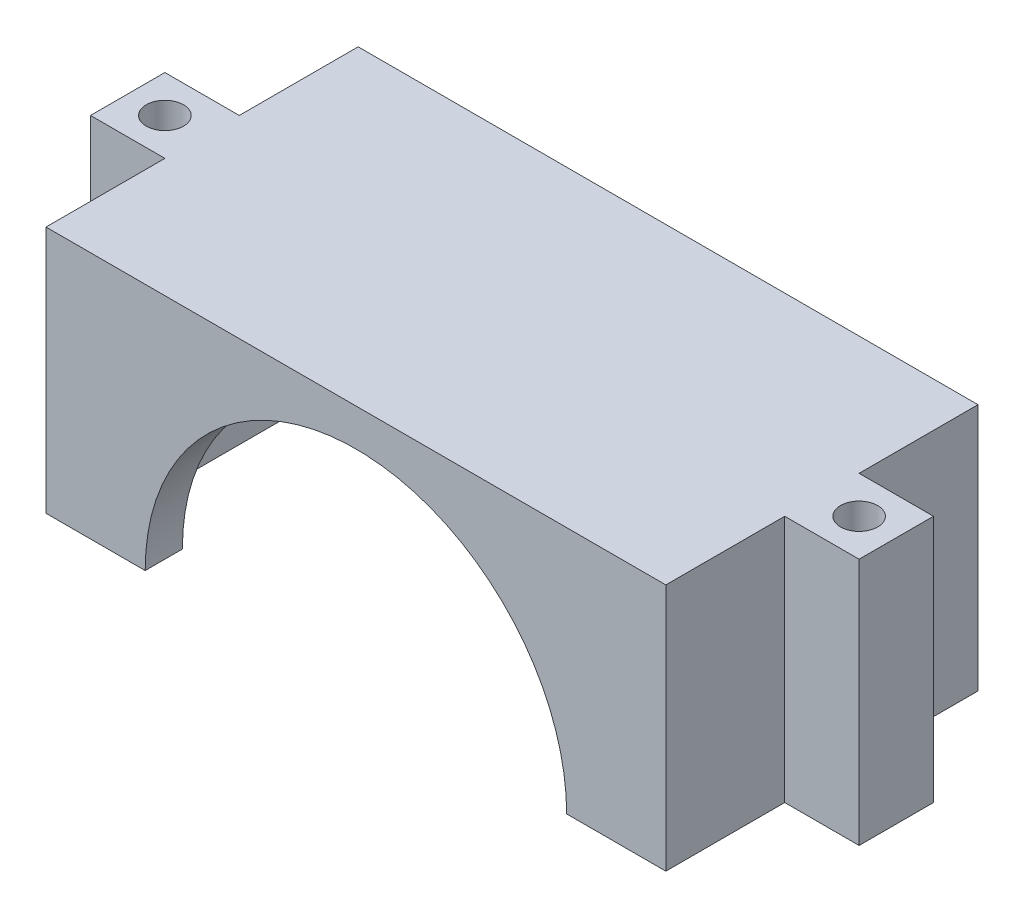
SolidWorks part; units mm, degrees
ref_plane "Front" through (0, 0, 0) normal (0, 0, 1) x (1, 0, 0)
ref_plane "Top" through (0, 0, 0) normal (0, 1, 0) x (1, 0, 0)
ref_plane "Right" through (0, 0, 0) normal (1, 0, 0) x (0, 0, -1)
sketch "Sketch1" plane through (0, 0, 0) normal (0, 1, 0) x (1, 0, 0)
  line L1 (-22, -9.59) -> (22, -9.59) construction
  line L2 (-22, -9.59) -> (-22, 9.59) construction
  line L3 (-22, 9.59) -> (22, 9.59) construction
  line L4 (22, -9.59) -> (22, 9.59) construction
  line L7 (-25, -12.59) -> (25, -12.59)
  line L8 (-25, -12.59) -> (-25, 12.59)
  line L9 (-25, 12.59) -> (25, 12.59)
  line L10 (25, -12.59) -> (25, 12.59)
  line L11 (-25, -12.59) -> (25, 12.59) construction
  line L12 (-25, 12.59) -> (25, -12.59) construction
  point P1 (0, 0)
  point P6 (0, 0)
  dimension "D1" = 44
  dimension "D2" = 19.18
  dimension "D3" = 50
  dimension "D4" = 25.18
  dimension "D5" = 3
extrude "Boss-Extrude1" add sketch "Sketch1" along normal blind 20
sketch "Sketch6" plane through (0, 0, 0) normal (0, -1, 0) x (1, 0, 0)
  line L1 (-22, -9.59) -> (22, -9.59)
  line L2 (-22, -9.59) -> (-22, 9.59)
  line L3 (-22, 9.59) -> (22, 9.59)
  line L4 (22, -9.59) -> (22, 9.59)
  line L5 (-22, -9.59) -> (22, 9.59) construction
  line L6 (-22, 9.59) -> (22, -9.59) construction
  point P0 (0, 0)
  dimension "D1" = 44
  dimension "D2" = 19.18
extrude "Cut-Extrude4" cut sketch "Sketch6" against normal blind 17
sketch "Sketch7" plane through (0, 0, 12.59) normal (0, 0, 1) x (1, 0, 0)
  line L0 (-25, 0) -> (25, 0) construction
  line L1 (-17, 0) -> (17, 0) construction
  line L2 (-17, 0) -> (17, 0)
  arc A0 (17, 0) -> (-17, 0) centre (0, 0) ccw
  point P0 (0, 0)
extrude "Cut-Extrude5" cut sketch "Sketch7" against normal up to surface (3 mm away) up to face at (0, 8.5, 9.59)
sketch "Sketch8" plane through (0, 0, -12.59) normal (0, 0, -1) x (-1, 0, 0)
  line L0 (-25, 20) -> (-25, 0) construction
  line L1 (-22, 0) -> (22, 0) construction
  line L2 (-22, 0) -> (-22, 17) construction
  line L3 (-22, 17) -> (22, 17) construction
  line L4 (22, 0) -> (22, 17) construction
  line L5 (-25, 0) -> (25, 0) construction
  line L6 (-22, 6) -> (-12, 6)
  line L7 (-12, 6) -> (-12, 0)
  line L8 (-22, 0) -> (-12, 0)
  line L9 (-22, 6) -> (-22, 0)
  line M1 (-25, 0) -> (25, 0)
  dimension "D1" = 3
  dimension "D2" = 0
  dimension "D3" = 44
  dimension "D4" = 17
  dimension "D5" = 10
  dimension "D6" = 6
extrude "Cut-Extrude6" cut sketch "Sketch8" against normal blind 17 contours L7 L6 L2 M1
sketch "Sketch9" plane through (0, 20, 0) normal (0, 1, 0) x (1, 0, 0)
  line L0 (25, -12.59) -> (25, 12.59) construction
  line L1 (0, 0) -> (0, -7.3144) construction
  line L2 (25, -3) -> (31, -3)
  line L3 (25, -3) -> (25, 3)
  line L4 (25, 3) -> (31, 3)
  line L5 (31, -3) -> (31, 3)
  line L6 (-25, -3) -> (-25, 3)
  line L7 (-25, -3) -> (-31, -3)
  line L8 (-31, -3) -> (-31, 3)
  line L9 (-25, 3) -> (-31, 3)
  circle A0 centre (28, 0) radius 1.5
  circle A1 centre (-28, 0) radius 1.5
  point P0 (25, -3)
  point P1 (25, 0)
  point P11 (31, 0)
  point P12 (28, 3)
  dimension "D4" = 3
  dimension "D1" = 3
  dimension "D2" = 6
  dimension "D3" = 6
extrude "Boss-Extrude2" add sketch "Sketch9" against normal blind 20
